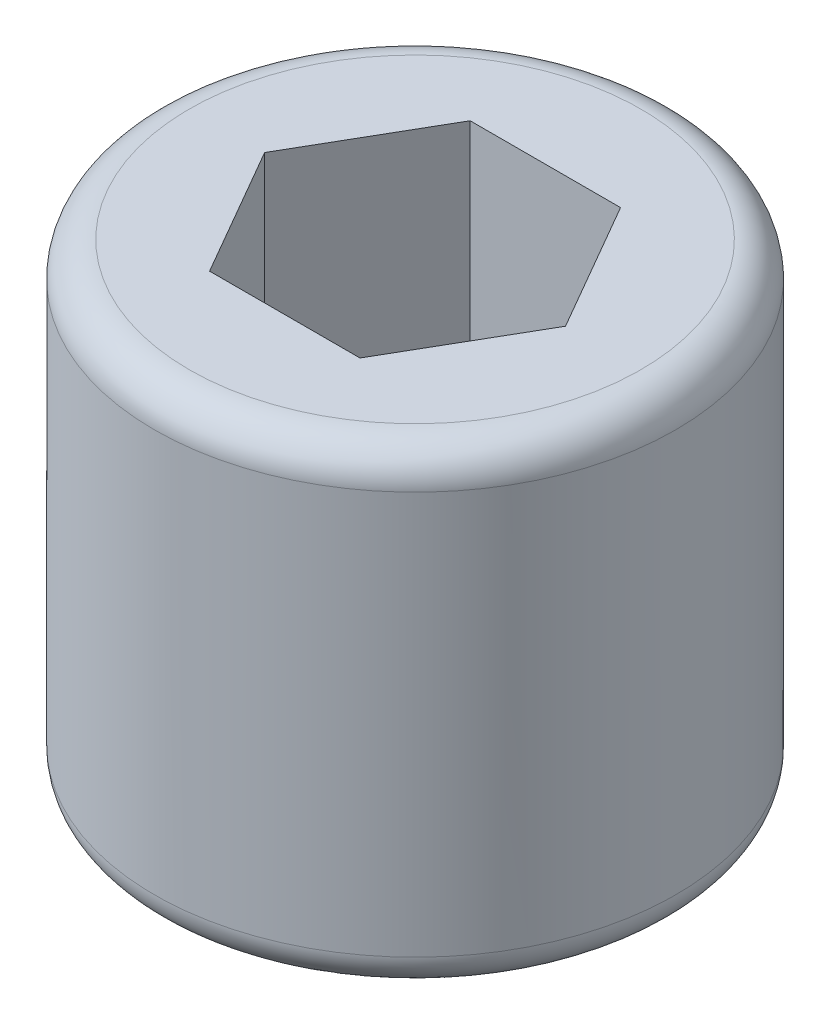
SolidWorks part; units mm, degrees
material "AISI 304"
ref_plane "前视基准面" through (0, 0, 0) normal (0, 0, 1) x (1, 0, 0)
ref_plane "上视基准面" through (0, 0, 0) normal (0, 1, 0) x (1, 0, 0)
ref_plane "右视基准面" through (0, 0, 0) normal (1, 0, 0) x (0, 0, -1)
sketch "草图1" plane through (0, 0, 0) normal (0, 1, 0) x (1, 0, 0)
  circle A0 centre (0, 0) radius 1.5
  dimension "D1" = 3
extrude "螺纹长度" add sketch "草图1" along normal blind 3
sketch "草图2" plane through (0, 3, 0) normal (0, 1, 0) x (1, 0, 0)
  line L1 (0.866, 0) -> (0.433, 0.75)
  line L2 (0.433, 0.75) -> (-0.433, 0.75)
  line L3 (-0.433, 0.75) -> (-0.866, 0)
  line L4 (-0.866, 0) -> (-0.433, -0.75)
  line L5 (-0.433, -0.75) -> (0.433, -0.75)
  line L6 (0.433, -0.75) -> (0.866, 0)
  circle A0 centre (0, 0) radius 0.75 construction
  point P1 (0, 0)
  dimension "D1" = 1.5
extrude "内六角深度" cut sketch "草图2" against normal blind 1.2
ref_axis "基准轴1" through (0, 3, 0) along (0, -1, 0)
sketch "草图3" plane through (0, 0, 0) normal (0, 0, 1) x (1, 0, 0)
  line L0 (0, -0.5) -> (0.866, 0) construction
  line L1 (1.5, 0) -> (1.5, 3) construction
  line L2 (1.5, 0.366) -> (1.5, 0)
  line L3 (1.5, -0.5) -> (0, -0.5) construction
  line L4 (0, 3) -> (0, 0) construction
  line L5 (-1.5, 0) -> (1.5, 0) construction
  line L6 (0.866, 0) -> (1.5, 0)
  line L7 (1.5, 0) -> (1.5, -0.5) construction
  line L8 (0.866, 0) -> (1.5, 0.366)
  point P9 (-0.6036, 1.6467)
  dimension "D1" = 60
  dimension "D2" = 0.5
revolve "切除-旋转4" cut sketch "草图3" angle 360 about axis through (0, 3, 0) along (0, -1, 0)
fillet "圆角1" radius 0.2 2 edges at (0, 3, 1.5) (0, 0.366, 1.5)
